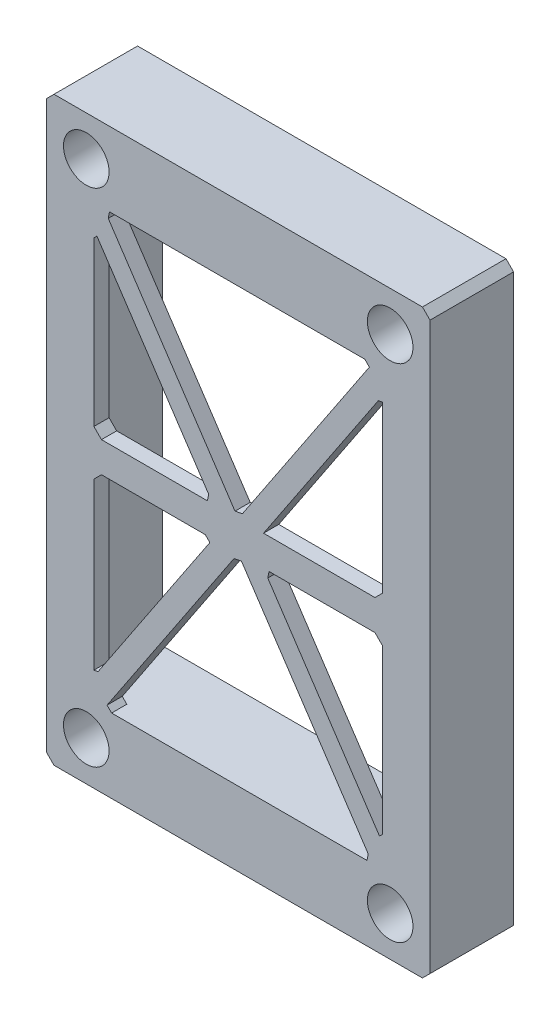
SolidWorks part; units mm, degrees
ref_plane "Front Plane" through (0, 0, 0) normal (0, 0, 1) x (1, 0, 0)
ref_plane "Top Plane" through (0, 0, 0) normal (0, 1, 0) x (1, 0, 0)
ref_plane "Right Plane" through (0, 0, 0) normal (1, 0, 0) x (0, 0, -1)
sketch "Sketch2" plane through (0, 0, 0) normal (0, 0, 1) x (1, 0, 0)
  line L0 (0, 0) -> (-9.5, 14.25) construction
  line L1 (-10, -16.5) -> (10, -16.5) construction
  line L2 (-10, -16.5) -> (-10, 16.5) construction
  line L3 (-10, 16.5) -> (10, 16.5) construction
  line L4 (10, -16.5) -> (10, 16.5) construction
  line L5 (-10, -16.5) -> (10, 16.5) construction
  line L6 (-10, 16.5) -> (10, -16.5) construction
  line L7 (12.625, -19.125) -> (-12.625, -19.125)
  line L8 (12.625, -19.125) -> (12.625, 19.125)
  line L9 (12.625, 19.125) -> (-12.625, 19.125)
  line L10 (-12.625, -19.125) -> (-12.625, 19.125)
  line L11 (12.625, -19.125) -> (-12.625, 19.125) construction
  line L12 (12.625, 19.125) -> (-12.625, -19.125) construction
  line L13 (9.5, -14.25) -> (-9.5, -14.25)
  line L14 (9.5, -14.25) -> (9.5, 14.25)
  line L15 (9.5, 14.25) -> (-9.5, 14.25)
  line L16 (-9.5, -14.25) -> (-9.5, 14.25)
  line L17 (9.5, -14.25) -> (-9.5, 14.25) construction
  line L18 (9.5, 14.25) -> (-9.5, -14.25) construction
  line L19 (-9.5, 12.75) -> (-1, 0)
  line L20 (-1, 0) -> (-9.5, -12.75)
  line L21 (-8.8333, -14.25) -> (0, -1)
  line L22 (0, -1) -> (8.8333, -14.25)
  line L23 (9.5, -12.75) -> (1, 0)
  line L24 (1, 0) -> (9.5, 12.75)
  line L25 (8.8333, 14.25) -> (0, 1)
  line L26 (0, 1) -> (-8.8333, 14.25)
  line L27 (-1, 0) -> (-9.5, 0) construction
  line L28 (1, 0) -> (9.5, 0) construction
  line L29 (-9.5, 1) -> (-1.6667, 1)
  line L30 (-1.6667, -1) -> (-9.5, -1)
  line L31 (9.5, -1) -> (1.6667, -1)
  line L32 (1.6667, 1) -> (9.5, 1)
  circle A0 centre (-10, 16.5) radius 1.5
  circle A1 centre (10, 16.5) radius 1.5
  circle A2 centre (10, -16.5) radius 1.5
  circle A3 centre (-10, -16.5) radius 1.5
  circle A4 centre (0, 0) radius 1
  point P0 (0, 0)
  point P10 (0, 0)
  point P15 (0, 0)
  dimension "D3" = 3
  dimension "D4" = 3
  dimension "D5" = 3
  dimension "D6" = 3
  dimension "D11" = 2
  dimension "D1" = 20
  dimension "D2" = 33
  dimension "D7" = 25.25
  dimension "D8" = 38.25
  dimension "D9" = 28.5
  dimension "D10" = 19
extrude "Boss-Extrude1" add sketch "Sketch2" along normal blind 3 contours A4 L26 L15 L16 L19 | A4 | A4 L24 L14 L15 L25 | L32 L24 L23 L31 L14 | A4 L22 L13 L14 L23 | A4 L20 L16 L13 L21 | L30 L20 L19 L29 L16 | L10 L7 L8 L9 A3 A2 A1 A0 L13 L16 L15 L14
chamfer "Chamfer1" distance 0.5 angle 45 21 edges at (-8.8333, -14.25, 1.5) (-9.5, -1, 1.5) (9.5, 12.75, 1.5) (-9.5, 12.75, 1.5) (0, -1, 1.5) (1.6667, -1, 1.5) (-8.8333, 14.25, 1.5) (-9.5, -12.75, 1.5) (-9.5, 1, 1.5) (0, 1, 1.5) (9.5, -12.75, 1.5) (-1.6667, 1, 1.5) (9.5, 1, 1.5) (8.8333, -14.25, 1.5) (9.5, -1, 1.5) (8.8333, 14.25, 1.5) (-1.6667, -1, 1.5) (-12.625, -19.125, 1.5) (12.625, -19.125, 1.5) (-12.625, 19.125, 1.5) (12.625, 19.125, 1.5)
sketch "Sketch3" plane through (0, 0, 0) normal (0, 0, -1) x (-1, 0, 0)
  line L0 (0, 0) -> (0, -19.125) construction
  line L1 (-12.125, -19.125) -> (12.125, -19.125) construction
  line L2 (10.5, -10.5) -> (-10.5, -10.5)
  line L3 (-10.5, -10.5) -> (-10.5, 10.5)
  line L4 (-10.5, 10.5) -> (10.5, 10.5)
  line L5 (10.5, 10.5) -> (10.5, -10.5)
  line L6 (-8.4728, -14.25) -> (8.3333, -14.25) construction
  line L7 (10.5, 14.25) -> (-10.5, 14.25)
  line L8 (10.5, 14.25) -> (10.5, -14.25)
  line L9 (10.5, -14.25) -> (-10.5, -14.25)
  line L10 (-10.5, 14.25) -> (-10.5, -14.25)
  line L11 (10.5, 14.25) -> (-10.5, -14.25) construction
  line L12 (10.5, -14.25) -> (-10.5, 14.25) construction
  circle A0 centre (-10, -16.5) radius 1.5 construction
  point P8 (0, -10.5)
  dimension "D1" = 6
  dimension "D2" = 21
  dimension "D3" = 21
extrude "Cut-Extrude1" cut sketch "Sketch3" against normal blind 2 contours L4 L5 L2 L3 | L10 L9 L8 L7
sketch "Sketch4" plane through (0, 0, 3) normal (0, 0, 1) x (1, 0, 0)
  line L0 (-12.625, -18.625) -> (-12.625, 18.625) construction
  line L1 (-12.625, -16.5) -> (-12.625, -19.125)
  line L2 (-12.625, -19.125) -> (-10, -19.125)
  line L3 (-10, -19.125) -> (-12.625, -16.5)
  line L4 (12.625, -16.5) -> (12.625, -19.125)
  line L5 (12.625, -19.125) -> (10, -19.125)
  line L6 (10, -19.125) -> (12.625, -16.5)
  line L7 (12.625, 21) -> (12.625, 19.125)
  line L8 (12.625, 19.125) -> (10, 19.125)
  line L9 (-12.625, 18.625) -> (-12.625, -18.625)
  line L10 (-12.625, -18.625) -> (-12.125, -19.125)
  line L11 (-12.125, -19.125) -> (12.125, -19.125)
  line L12 (12.125, -19.125) -> (12.625, -18.625)
  line L13 (12.625, -18.625) -> (12.625, 18.625)
  line L14 (12.625, 18.625) -> (12.125, 19.125)
  line L15 (12.125, 19.125) -> (-12.125, 19.125)
  line L16 (-12.125, 19.125) -> (-12.625, 18.625)
  line L17 (-12.625, 18.625) -> (-12.625, -18.625)
  line L18 (-12.625, -18.625) -> (-12.125, -19.125)
  line L19 (-12.125, -19.125) -> (12.125, -19.125)
  line L20 (12.125, -19.125) -> (12.625, -18.625)
  line L21 (12.625, -18.625) -> (12.625, 18.625)
  line L22 (12.625, 18.625) -> (12.125, 19.125)
  line L23 (12.125, 19.125) -> (-12.125, 19.125)
  line L24 (-12.125, 19.125) -> (-12.625, 18.625)
  line L25 (10, 19.125) -> (12.625, 21)
  line L26 (-12.625, 21) -> (-12.625, 19.125)
  line L27 (-12.625, 19.125) -> (-10, 19.125)
  line L28 (-10, 19.125) -> (-12.625, 21)
  circle A0 centre (-10, -16.5) radius 1.5 construction
  circle A1 centre (10, -16.5) radius 1.5 construction
  circle A2 centre (10, 16.5) radius 1.5 construction
  circle A3 centre (-10, 16.5) radius 1.5 construction
  circle A4 centre (-10, -16.5) radius 1.5
  circle A5 centre (10, -16.5) radius 1.5
  circle A6 centre (10, 16.5) radius 1.5
  circle A7 centre (-10, 16.5) radius 1.5
  circle A8 centre (-10, 16.5) radius 2.625
  circle A9 centre (10, 16.5) radius 2.625
  circle A10 centre (-10, -16.5) radius 2.625
  circle A11 centre (10, -16.5) radius 2.625
  dimension "D1" = 0
sketch "Sketch5" plane through (0, 0, 0) normal (0, 0, -1) x (-1, 0, 0)
  line L0 (-10.5, -14.25) -> (10.5, -14.25) construction
  line L1 (10.5, 14.25) -> (10.5, -14.25) construction
  line L2 (-10.5, 14.25) -> (10.5, 14.25) construction
  line L3 (-10.5, -14.25) -> (-10.5, 14.25) construction
  line L4 (-10.5, -14.25) -> (10.5, -14.25)
  line L5 (10.5, 14.25) -> (10.5, -14.25)
  line L6 (-10.5, 14.25) -> (10.5, 14.25)
  line L7 (-10.5, -14.25) -> (-10.5, 14.25)
  line L8 (-12.125, -19.125) -> (12.125, -19.125)
  line L9 (12.125, -19.125) -> (12.625, -18.625)
  line L10 (12.625, -18.625) -> (12.625, 18.625)
  line L11 (12.625, 18.625) -> (12.125, 19.125)
  line L12 (12.125, 19.125) -> (-12.125, 19.125)
  line L13 (-12.125, 19.125) -> (-12.625, 18.625)
  line L14 (-12.625, 18.625) -> (-12.625, -18.625)
  line L15 (-12.625, -18.625) -> (-12.125, -19.125)
  line L16 (-12.125, -19.125) -> (12.125, -19.125)
  line L17 (12.125, -19.125) -> (12.625, -18.625)
  line L18 (12.625, -18.625) -> (12.625, 18.625)
  line L19 (12.625, 18.625) -> (12.125, 19.125)
  line L20 (12.125, 19.125) -> (-12.125, 19.125)
  line L21 (-12.125, 19.125) -> (-12.625, 18.625)
  line L22 (-12.625, 18.625) -> (-12.625, -18.625)
  line L23 (-12.625, -18.625) -> (-12.125, -19.125)
  circle A0 centre (-10, -16.5) radius 1.5 construction
  circle A1 centre (10, -16.5) radius 1.5 construction
  circle A2 centre (10, 16.5) radius 1.5 construction
  circle A3 centre (-10, 16.5) radius 1.5 construction
  circle A4 centre (-10, -16.5) radius 1.5
  circle A5 centre (10, -16.5) radius 1.5
  circle A6 centre (10, 16.5) radius 1.5
  circle A7 centre (-10, 16.5) radius 1.5
  dimension "D1" = 0
extrude "Boss-Extrude2" add sketch "Sketch5" along normal blind 2.5
